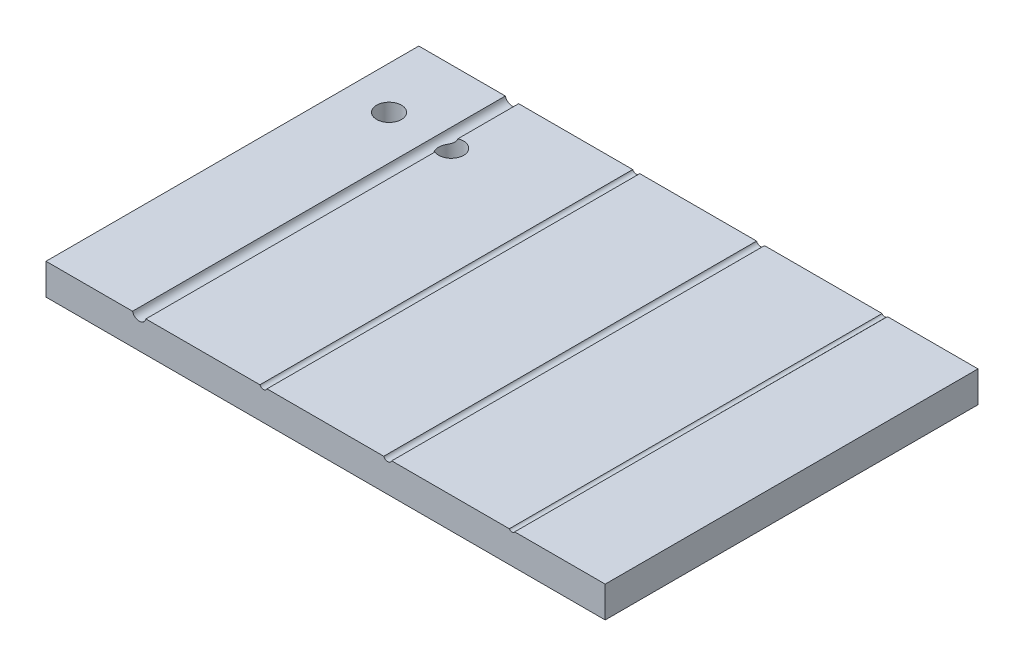
SolidWorks part; units mm, degrees
ref_plane "Front Plane" through (0, 0, 0) normal (0, 0, 1) x (1, 0, 0)
ref_plane "Top Plane" through (0, 0, 0) normal (0, 1, 0) x (1, 0, 0)
ref_plane "Right Plane" through (0, 0, 0) normal (1, 0, 0) x (0, 0, -1)
sketch "Sketch1" plane through (0, 0, 0) normal (0, 1, 0) x (1, 0, 0)
  line L1 (-60.7547, 92.0755) -> (29.2453, 92.0755)
  line L2 (-60.7547, 92.0755) -> (-60.7547, 32.0755)
  line L3 (-60.7547, 32.0755) -> (29.2453, 32.0755)
  line L4 (29.2453, 92.0755) -> (29.2453, 32.0755)
  dimension "D1" = 60
  dimension "D2" = 90
extrude "Boss-Extrude1" add sketch "Sketch1" along normal blind 5
sketch "Sketch2" plane through (0, 0, -32.0755) normal (0, 0, 1) x (1, 0, 0)
  line L0 (-60.7547, 5) -> (29.2453, 5) construction
  line L1 (-45.7547, 6.7696) -> (-45.7547, 3.4135) construction
  line L2 (-45.7547, 5.25) -> (-25.7547, 5.25) construction
  line L3 (-25.7547, 5.25) -> (14.2453, 5.25) construction
  circle A0 centre (-45.7547, 5.25) radius 1.1
  circle A1 centre (-25.7547, 5.25) radius 0.62
  circle A2 centre (-5.7547, 5.25) radius 0.6858
  circle A3 centre (14.2453, 5.25) radius 0.5
  point P6 (-15.7547, 5)
  dimension "D2" = 2.2
  dimension "D3" = 1.24
  dimension "D5" = 1.3716
  dimension "D6" = 1
  dimension "D1" = 0.25
  dimension "D4" = 20
  dimension "D7" = 20
  dimension "D8" = 20
  dimension "D9" = 15
extrude "Cut-Extrude1" cut sketch "Sketch2" against normal through all contours A0 | A1 | A3 | A2
sketch "Sketch3" plane through (0, 5, 0) normal (0, 1, 0) x (1, 0, 0)
  line L8 (-45.7547, 92.0755) -> (-45.7547, 32.0755) construction
  line L9 (-25.7547, 92.0755) -> (-25.7547, 30.7197) construction
  line L10 (-5.7547, 92.0755) -> (-5.7547, 32.0755) construction
  line L11 (14.2453, 92.0755) -> (14.2453, 32.0755) construction
  line L12 (-60.7547, 62.0755) -> (29.2453, 62.0755) construction
  line L13 (-60.7547, 92.0755) -> (-60.7547, 32.0755) construction
  line L15 (29.2453, 32.0755) -> (29.2453, 92.0755) construction
  circle A0 centre (-53.9074, 80.4423) radius 2
  circle A1 centre (-43.9074, 80.4423) radius 2
  dimension "D2" = 10
  dimension "D1" = 4
extrude "Cut-Extrude2" cut sketch "Sketch3" against normal through all
